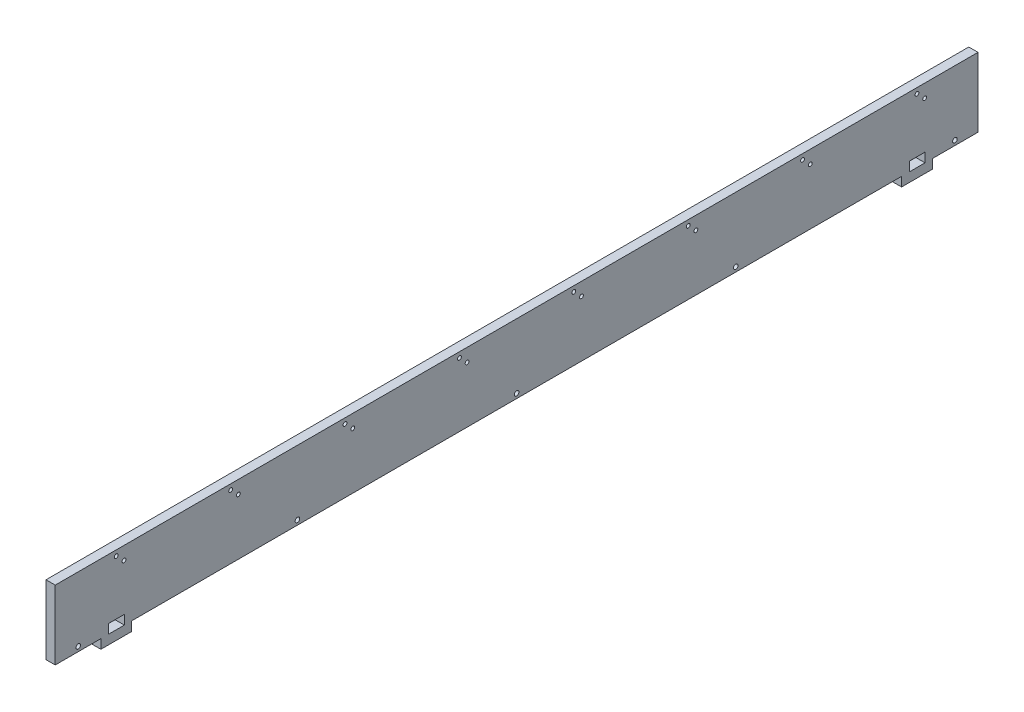
SolidWorks part; units mm, degrees
ref_plane "Front Plane" through (0, 0, 0) normal (0, 0, 1) x (1, 0, 0)
ref_plane "Top Plane" through (0, 0, 0) normal (0, 1, 0) x (1, 0, 0)
ref_plane "Right Plane" through (0, 0, 0) normal (1, 0, 0) x (0, 0, -1)
sketch "Sketch1" plane through (0, 0, 0) normal (1, 0, 0) x (0, 0, -1)
  line L1 (0, 0) -> (1220, 0)
  line L2 (0, 0) -> (0, 102)
  line L3 (0, 102) -> (1220, 102)
  line L4 (1220, 0) -> (1220, 102)
  dimension "D1" = 102
  dimension "D2" = 1220
extrude "Boss-Extrude1" add sketch "Sketch1" along normal blind 12
sketch "Sketch3" plane through (12, 0, 0) normal (1, 0, 0) x (0, 0, -1)
  line L0 (89.375, 101.0792) -> (89.375, -67.7303)
  line L1 (20, 101.0792) -> (158.75, 101.0792)
  line L2 (20, 101.0792) -> (20, -67.7303)
  line L3 (20, -67.7303) -> (158.75, -67.7303)
  line L4 (158.75, 101.0792) -> (158.75, -67.7303)
  line L5 (238.125, 101.0792) -> (238.125, -67.7303)
  line L6 (168.75, 101.0792) -> (307.5, 101.0792)
  line L7 (168.75, 101.0792) -> (168.75, -67.7303)
  line L8 (168.75, -67.7303) -> (307.5, -67.7303)
  line L9 (307.5, 101.0792) -> (307.5, -67.7303)
  line L10 (386.875, 101.0792) -> (386.875, -67.7303)
  line L11 (317.5, 101.0792) -> (456.25, 101.0792)
  line L12 (317.5, 101.0792) -> (317.5, -67.7303)
  line L13 (317.5, -67.7303) -> (456.25, -67.7303)
  line L14 (456.25, 101.0792) -> (456.25, -67.7303)
  line L15 (535.625, 101.0792) -> (535.625, -67.7303)
  line L16 (466.25, 101.0792) -> (605, 101.0792)
  line L17 (466.25, 101.0792) -> (466.25, -67.7303)
  line L18 (466.25, -67.7303) -> (605, -67.7303)
  line L19 (605, 101.0792) -> (605, -67.7303)
  line L20 (684.375, 101.0792) -> (684.375, -67.7303)
  line L21 (615, 101.0792) -> (753.75, 101.0792)
  line L22 (615, 101.0792) -> (615, -67.7303)
  line L23 (615, -67.7303) -> (753.75, -67.7303)
  line L24 (753.75, 101.0792) -> (753.75, -67.7303)
  line L25 (833.125, 101.0792) -> (833.125, -67.7303)
  line L26 (763.75, 101.0792) -> (902.5, 101.0792)
  line L27 (763.75, 101.0792) -> (763.75, -67.7303)
  line L28 (763.75, -67.7303) -> (902.5, -67.7303)
  line L29 (902.5, 101.0792) -> (902.5, -67.7303)
  line L30 (981.875, 101.0792) -> (981.875, -67.7303)
  line L31 (912.5, 101.0792) -> (1051.25, 101.0792)
  line L32 (912.5, 101.0792) -> (912.5, -67.7303)
  line L33 (912.5, -67.7303) -> (1051.25, -67.7303)
  line L34 (1051.25, 101.0792) -> (1051.25, -67.7303)
  line L35 (1130.625, 101.0792) -> (1130.625, -67.7303)
  line L36 (1061.25, 101.0792) -> (1200, 101.0792)
  line L37 (1061.25, 101.0792) -> (1061.25, -67.7303)
  line L38 (1061.25, -67.7303) -> (1200, -67.7303)
  line L39 (1200, 101.0792) -> (1200, -67.7303)
  line L40 (0, 102) -> (0, 0) construction
  line L41 (1220, 0) -> (1220, 102) construction
  dimension "D2" = 20
  dimension "D3" = 10
  dimension "D4" = 20
  dimension "D1" = 8
sketch "Sketch4" plane through (12, 0, 0) normal (1, 0, 0) x (0, 0, -1)
  line L0 (0, 0) -> (1220, 0) construction
  line L1 (-14.9337, 12) -> (69.375, 12)
  line L2 (-14.9337, 12) -> (-14.9337, -24.2801)
  line L3 (-14.9337, -24.2801) -> (69.375, -24.2801)
  line L4 (69.375, 12) -> (69.375, -24.2801)
  line L5 (109.375, -30.9633) -> (1110.625, -30.9633)
  line L6 (109.375, -30.9633) -> (109.375, 12)
  line L7 (109.375, 12) -> (1110.625, 12)
  line L8 (1110.625, -30.9633) -> (1110.625, 12)
  line L9 (1150.625, -30.9633) -> (1263.3607, -30.9633)
  line L10 (1150.625, -30.9633) -> (1150.625, 12)
  line L11 (1150.625, 12) -> (1263.3607, 12)
  line L12 (1263.3607, -30.9633) -> (1263.3607, 12)
  line L13 (89.375, 101.0792) -> (89.375, -67.7303) construction
  line L14 (1130.625, 101.0792) -> (1130.625, -67.7303) construction
  dimension "D1" = 12
  dimension "D2" = 20
  dimension "D3" = 20
  dimension "D4" = 20
  dimension "D5" = 20
extrude "Cut-Extrude1" cut sketch "Sketch4" against normal blind 20
sketch "Sketch5" plane through (12, 0, 0) normal (1, 0, 0) x (0, 0, -1)
  line L0 (1220, 12) -> (1220, 102) construction
  line L1 (1210, 106.509) -> (1317.1067, 106.509)
  line L2 (1210, 106.509) -> (1210, -57.6437)
  line L3 (1210, -57.6437) -> (1317.1067, -57.6437)
  line L4 (1317.1067, 106.509) -> (1317.1067, -57.6437)
  line L5 (-99.4351, 119.3153) -> (10, 119.3153)
  line L6 (-99.4351, 119.3153) -> (-99.4351, -57.6437)
  line L7 (-99.4351, -57.6437) -> (10, -57.6437)
  line L8 (10, 119.3153) -> (10, -57.6437)
  line L9 (0, 102) -> (0, 12) construction
  dimension "D1" = 10
  dimension "D2" = 10
extrude "Cut-Extrude2" cut sketch "Sketch5" against normal blind 20
sketch "Sketch6" plane through (12, 0, 0) normal (1, 0, 0) x (0, 0, -1)
  line L0 (89.375, 101.0792) -> (89.375, -67.7303) construction
  line L2 (1130.625, 101.0792) -> (1130.625, -67.7303) construction
  line L3 (1210, 102) -> (10, 102) construction
  circle A0 centre (89.375, 95) radius 2.5
  circle A1 centre (238.125, 95) radius 2.5
  circle A2 centre (386.875, 95) radius 2.5
  circle A3 centre (535.625, 95) radius 2.5
  circle A4 centre (684.375, 95) radius 2.5
  circle A5 centre (833.125, 95) radius 2.5
  circle A6 centre (981.875, 95) radius 2.5
  circle A7 centre (1130.625, 95) radius 2.5
  dimension "D1" = 5
  dimension "D3" = 7
  dimension "D2" = 8
extrude "Cut-Extrude3" cut sketch "Sketch6" against normal blind 20
sketch "Sketch7" plane through (12, 0, 0) normal (1, 0, 0) x (0, 0, -1)
  circle A0 centre (99.375, 85) radius 2.5
  circle A1 centre (89.375, 95) radius 2.5 construction
  circle A2 centre (248.125, 85) radius 2.5
  circle A3 centre (396.875, 85) radius 2.5
  circle A4 centre (545.625, 85) radius 2.5
  circle A5 centre (694.375, 85) radius 2.5
  circle A6 centre (843.125, 85) radius 2.5
  circle A7 centre (991.875, 85) radius 2.5
  circle A8 centre (1140.625, 85) radius 2.5
  circle A9 centre (1130.625, 95) radius 2.5 construction
  dimension "D1" = 5
  dimension "D2" = 10
  dimension "D3" = 10
  dimension "D4" = 10
  dimension "D5" = 8
  dimension "D6" = 10
extrude "Cut-Extrude4" cut sketch "Sketch7" against normal blind 22
sketch "Sketch8" plane through (12, 0, 0) normal (1, 0, 0) x (0, 0, -1)
  line L0 (69.375, 0) -> (69.375, 12) construction
  line L1 (79.375, 12) -> (99.875, 12)
  line L2 (79.375, 12) -> (79.375, 24.1)
  line L3 (79.375, 24.1) -> (99.875, 24.1)
  line L4 (99.875, 12) -> (99.875, 24.1)
  line L5 (69.375, 12) -> (10, 12) construction
  line L6 (1120.625, 12) -> (1141.125, 12)
  line L7 (1120.625, 12) -> (1120.625, 24.1)
  line L8 (1120.625, 24.1) -> (1141.125, 24.1)
  line L9 (1141.125, 12) -> (1141.125, 24.1)
  line L10 (1110.625, 12) -> (109.375, 12) construction
  line L11 (1110.625, 0) -> (1110.625, 12) construction
  dimension "D1" = 20.5
  dimension "D2" = 12.1
  dimension "D3" = 10
  dimension "D5" = 10
  dimension "D6" = 1041.25
  dimension "D4" = 2
extrude "Cut-Extrude5" cut sketch "Sketch8" against normal blind 20
sketch "Sketch9" plane through (12, 0, 0) normal (1, 0, 0) x (0, 0, -1)
  line L0 (10, 12) -> (10, 102) construction
  line L1 (69.375, 0) -> (69.375, 12) construction
  line L2 (69.375, 12) -> (10, 12) construction
  line L3 (1210, 102) -> (1210, 12) construction
  line L4 (1210, 12) -> (1150.625, 12) construction
  circle A0 centre (40, 18) radius 3
  circle A1 centre (325, 18) radius 3
  circle A2 centre (610, 18) radius 3
  circle A3 centre (895, 18) radius 3
  circle A4 centre (1180, 18) radius 3
  dimension "D1" = 6
  dimension "D2" = 30
  dimension "D3" = 29.375
  dimension "D4" = 6
  dimension "D5" = 30
  dimension "D6" = 5
  dimension "D7" = 6
extrude "Cut-Extrude6" cut sketch "Sketch9" against normal blind 20
